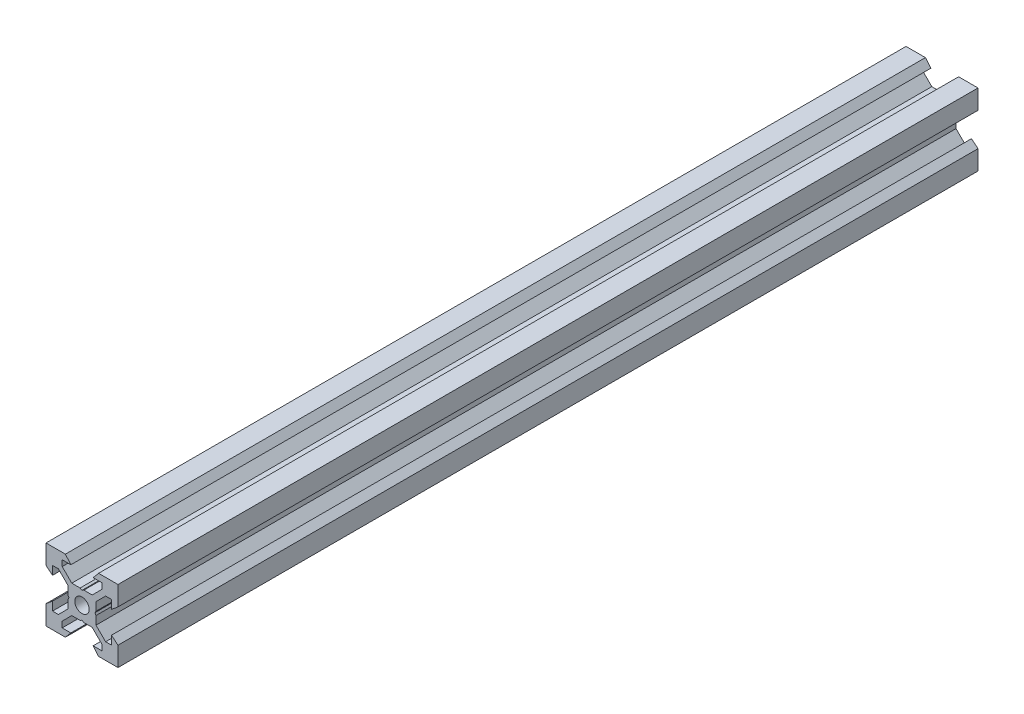
SolidWorks part; units mm, degrees
ref_plane "Front Plane" through (0, 0, 0) normal (0, 0, 1) x (1, 0, 0)
ref_plane "Top Plane" through (0, 0, 0) normal (0, 1, 0) x (1, 0, 0)
ref_plane "Right Plane" through (0, 0, 0) normal (1, 0, 0) x (0, 0, -1)
sketch "Sketch1" plane through (0, 0, 0) normal (0, 0, 1) x (1, 0, 0)
  line L0 (10, 10) -> (4.6104, 10) construction
  line L1 (10, 10) -> (10, 4.6104) construction
  line L2 (10, -10) -> (10, -4.6104) construction
  line L3 (10, -10) -> (4.6104, -10) construction
  line L4 (10, 10) -> (10, 4.6104)
  line L5 (6.5607, 5.5) -> (8.2, 5.5)
  line L6 (5.5, 8.2) -> (5.5, 6.5607)
  line L7 (10, 10) -> (4.6104, 10)
  line L8 (10, 10) -> (10, 4.6104)
  line L9 (6.5607, 5.5) -> (3.9, 2.8393)
  line L10 (5.5, 6.5607) -> (2.8393, 3.9)
  line L11 (10, 4.6104) -> (8.2, 3.1)
  line L12 (4.6104, 10) -> (3.1, 8.2)
  line L13 (8.2, 3.1) -> (8.2, 5.5)
  line L14 (3.1, 8.2) -> (5.5, 8.2)
  line L15 (-6.5607, 5.5) -> (-8.2, 5.5)
  line L16 (6.5607, -5.5) -> (8.2, -5.5)
  line L17 (3.1, -8.2) -> (5.5, -8.2)
  line L18 (8.2, -3.1) -> (8.2, -5.5)
  line L19 (4.6104, -10) -> (3.1, -8.2)
  line L20 (10, -4.6104) -> (8.2, -3.1)
  line L21 (0.5196, -3.9) -> (0, -3.6)
  line L22 (0.5196, 3.9) -> (0, 3.6)
  line L23 (3.6, 0) -> (3.9, -0.5196)
  line L24 (3.9, 0.5196) -> (3.6, 0)
  line L25 (3.9, 0.5196) -> (3.9, 2.8393)
  line L26 (2.8393, 3.9) -> (0.5196, 3.9)
  line L27 (3.9, -2.8393) -> (3.9, -0.5196)
  line L28 (2.8393, -3.9) -> (0.5196, -3.9)
  line L29 (5.5, -6.5607) -> (2.8393, -3.9)
  line L30 (6.5607, -5.5) -> (3.9, -2.8393)
  line L31 (10, -10) -> (10, -4.6104)
  line L32 (10, -10) -> (4.6104, -10)
  line L33 (5.5, -8.2) -> (5.5, -6.5607)
  line L34 (-6.5607, -5.5) -> (-8.2, -5.5)
  line L35 (10, -10) -> (10, -4.6104)
  line L36 (0, 0) -> (0, 8.2) construction
  line L37 (-10, -10) -> (-4.6104, -10) construction
  line L38 (-10, -10) -> (-10, -4.6104) construction
  line L39 (-10, 10) -> (-10, 4.6104) construction
  line L40 (-10, 10) -> (-4.6104, 10) construction
  line L41 (-10, -10) -> (-10, -4.6104)
  line L43 (-5.5, -8.2) -> (-5.5, -6.5607)
  line L44 (-10, -10) -> (-4.6104, -10)
  line L45 (-10, -10) -> (-10, -4.6104)
  line L46 (-6.5607, -5.5) -> (-3.9, -2.8393)
  line L47 (-5.5, -6.5607) -> (-2.8393, -3.9)
  line L48 (-2.8393, -3.9) -> (-0.5196, -3.9)
  line L49 (-3.9, -2.8393) -> (-3.9, -0.5196)
  line L50 (-2.8393, 3.9) -> (-0.5196, 3.9)
  line L51 (-3.9, 0.5196) -> (-3.9, 2.8393)
  line L52 (-3.9, 0.5196) -> (-3.6, 0)
  line L53 (-3.6, 0) -> (-3.9, -0.5196)
  line L54 (-0.5196, 3.9) -> (0, 3.6)
  line L55 (-0.5196, -3.9) -> (0, -3.6)
  line L56 (-10, -4.6104) -> (-8.2, -3.1)
  line L57 (-4.6104, -10) -> (-3.1, -8.2)
  line L58 (-8.2, -3.1) -> (-8.2, -5.5)
  line L59 (-3.1, -8.2) -> (-5.5, -8.2)
  line L60 (-10, -10) -> (10, -10) construction
  line L61 (-10, -10) -> (-10, 10) construction
  line L62 (-3.1, 8.2) -> (-5.5, 8.2)
  line L63 (-8.2, 3.1) -> (-8.2, 5.5)
  line L64 (-4.6104, 10) -> (-3.1, 8.2)
  line L65 (-10, 4.6104) -> (-8.2, 3.1)
  line L66 (-5.5, 6.5607) -> (-2.8393, 3.9)
  line L67 (-6.5607, 5.5) -> (-3.9, 2.8393)
  line L68 (-10, 10) -> (-10, 4.6104)
  line L69 (-10, 10) -> (-4.6104, 10)
  line L70 (-5.5, 8.2) -> (-5.5, 6.5607)
  line L71 (-10, 10) -> (10, 10) construction
  line L72 (-10, 10) -> (-10, 4.6104)
  line L73 (10, -10) -> (10, 10) construction
  line L74 (-10, -10) -> (10, 10) construction
  line L75 (-10, 10) -> (10, -10) construction
  circle A0 centre (0, 0) radius 2
  dimension "D7" = 4
  dimension "D1" = 20
  dimension "D2" = 5.3896
  dimension "D3" = 4.5
  dimension "D4" = 50
  dimension "D5" = 1.8
  dimension "D6" = 1.5104
  dimension "D8" = 5.5
  dimension "D9" = 120
  dimension "D10" = 0.3
  dimension "D11" = 2.3197
  dimension "D12" = 7.8
  dimension "D13" = 7.8
  dimension "D14" = 1.5
  dimension "D15" = 2.6607
extrude "Boss-Extrude1" add sketch "Sketch1" along normal mid plane 239 contours L70 L62 L64 L69 L68 L65 L63 L15 L67 L51 L52 L53 L49 L46 L34 L58 L56 L41 L44 L57 L59 L43 L47 L48 L55 L21 L28 L29 L33 L17 L19 L32 L31 L20 L18 L16 L30 L27 L23 L24 L25 L9 L5 L13 L11 L4 L7 L12 L14 L6 L10
